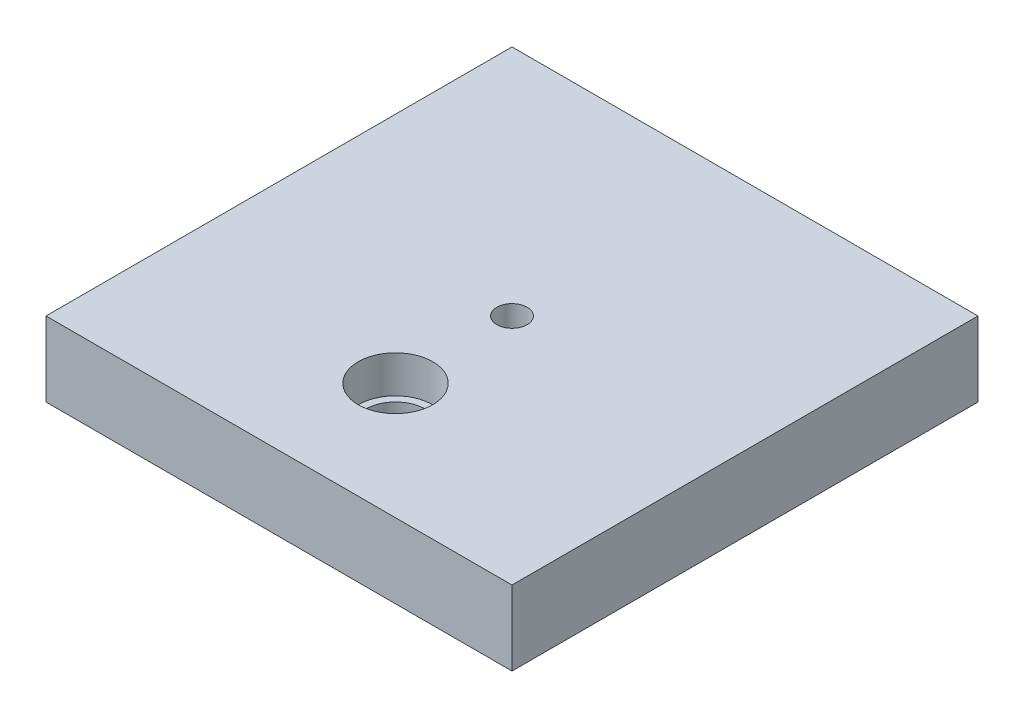
SolidWorks part; units mm, degrees
ref_plane "Front Plane" through (0, 0, 0) normal (0, 0, 1) x (1, 0, 0)
ref_plane "Top Plane" through (0, 0, 0) normal (0, 1, 0) x (1, 0, 0)
ref_plane "Right Plane" through (0, 0, 0) normal (1, 0, 0) x (0, 0, -1)
sketch "Sketch1" plane through (0, 0, 0) normal (0, 1, 0) x (1, 0, 0)
  line L0 (0, 50) -> (0, -50) construction
  line L1 (-50, 50) -> (50, 50)
  line L2 (-50, 50) -> (-50, -50)
  line L3 (-50, -50) -> (50, -50)
  line L4 (50, 50) -> (50, -50)
  line L5 (-50, 50) -> (50, -50) construction
  line L6 (-50, -50) -> (50, 50) construction
  circle A0 centre (0, 0) radius 3.25
  point P0 (0, 0)
  dimension "D3" = 6.5
  dimension "D1" = 100
  dimension "D2" = 100
extrude "Boss-Extrude1" add sketch "Sketch1" along normal blind 16
ref_point "Center point"
sketch "Sketch2" plane through (0, 16, 0) normal (0, 1, 0) x (1, 0, 0)
  line L0 (0, 50) -> (0, -50) construction
  line L1 (50, 50) -> (-50, 50) construction
  line L2 (-50, -50) -> (50, -50) construction
  circle A0 centre (0, -25) radius 8
  dimension "D1" = 16
  dimension "D2" = 25
extrude "Cut-Extrude1" cut sketch "Sketch2" against normal blind 8
sketch "Sketch3" plane through (0, 8, 0) normal (0, 1, 0) x (1, 0, 0)
  circle A0 centre (0, -25) radius 6.4
  dimension "D1" = 12.8
extrude "Cut-Extrude2" cut sketch "Sketch3" against normal up to next
